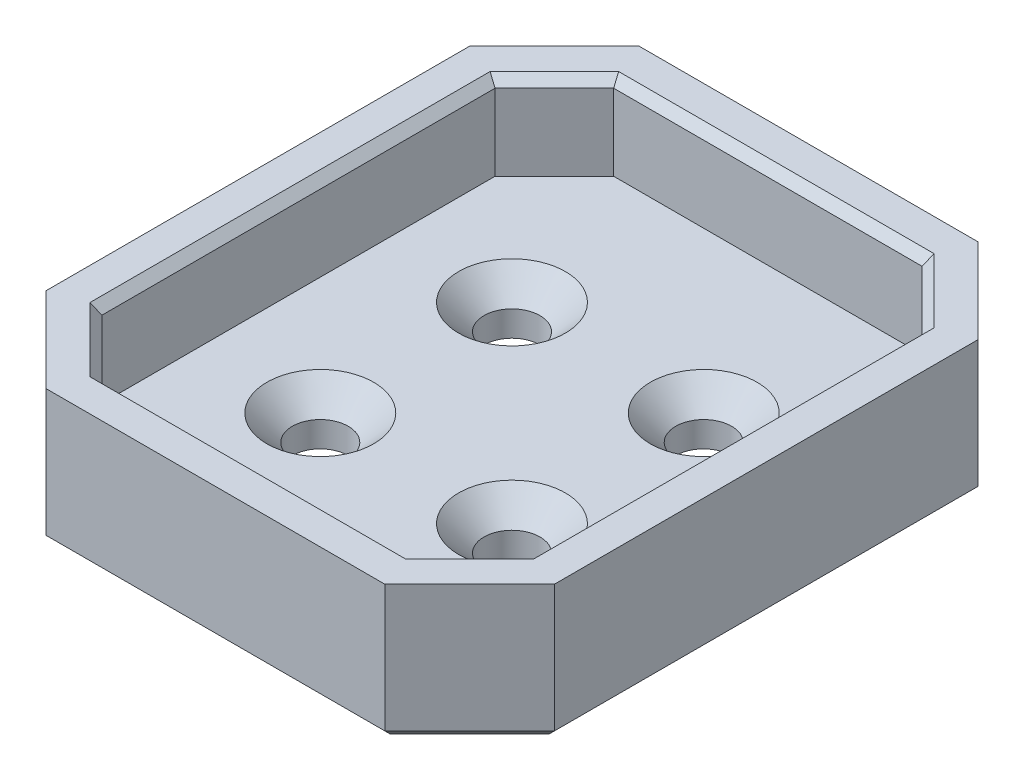
SolidWorks part; units mm, degrees
ref_plane "Front Plane" through (0, 0, 0) normal (0, 0, 1) x (1, 0, 0)
ref_plane "Top Plane" through (0, 0, 0) normal (0, 1, 0) x (1, 0, 0)
ref_plane "Right Plane" through (0, 0, 0) normal (1, 0, 0) x (0, 0, -1)
sketch "Sketch1" plane through (0, 0, 0) normal (0, 1, 0) x (1, 0, 0)
  line L1 (-15, -17.5) -> (15, -17.5)
  line L2 (-15, -17.5) -> (-15, 17.5)
  line L3 (-15, 17.5) -> (15, 17.5)
  line L4 (15, -17.5) -> (15, 17.5)
  line L5 (-15, -17.5) -> (15, 17.5) construction
  line L6 (-15, 17.5) -> (15, -17.5) construction
  point P0 (0, 0)
  dimension "D1" = 35
  dimension "D2" = 30
extrude "Boss-Extrude1" add sketch "Sketch1" along normal blind 3
sketch "Sketch2" plane through (0, 3, 0) normal (0, 1, 0) x (1, 0, 0)
  line L1 (12.6, -11.6) -> (12.6, 11.6)
  line L2 (9.1, 15.1) -> (-9.1, 15.1)
  line L3 (-12.6, 11.6) -> (-12.6, -11.6)
  line L4 (-9.1, -15.1) -> (9.1, -15.1)
  line L5 (15, -17.5) -> (15, 17.5)
  line L6 (15, 17.5) -> (-15, 17.5)
  line L7 (-15, 17.5) -> (-15, -17.5)
  line L8 (-15, -17.5) -> (15, -17.5)
  line L9 (15, -17.5) -> (15, 17.5)
  line L10 (15, 17.5) -> (-15, 17.5)
  line L11 (-15, 17.5) -> (-15, -17.5)
  line L12 (-15, -17.5) -> (15, -17.5)
  line L13 (12.6, 15.1) -> (-12.6, 15.1) construction
  line L14 (-12.6, 15.1) -> (-12.6, -15.1) construction
  line L15 (-9.1, 15.1) -> (-12.6, 11.6)
  line L16 (12.6, -15.1) -> (12.6, 15.1) construction
  line L17 (12.6, 11.6) -> (9.1, 15.1)
  line L18 (-12.6, -15.1) -> (12.6, -15.1) construction
  line L19 (9.1, -15.1) -> (12.6, -11.6)
  line L20 (-12.6, -11.6) -> (-9.1, -15.1)
  dimension "D3" = 3.5
  dimension "D4" = 3.5
  dimension "D1" = 0
  dimension "D2" = 2.4
extrude "Boss-Extrude2" add sketch "Sketch2" along normal blind 5
chamfer "Chamfer1" distance 5 angle 45 4 edges at (15, 4, 17.5) (-15, 4, 17.5) (15, 4, -17.5) (-15, 4, -17.5)
sketch "Sketch4" plane through (0, 3, 0) normal (0, 1, 0) x (1, 0, 0)
  line L0 (-5.6569, 5.6569) -> (0, 0) construction
  line L1 (0, 0) -> (0, 15.1) construction
  line L2 (9.1, 15.1) -> (-9.1, 15.1) construction
  circle A0 centre (0, 0) radius 8 construction
  circle A1 centre (-5.6569, 5.6569) radius 1.5
  circle A2 centre (5.6569, 5.6569) radius 1.5
  circle A3 centre (5.6569, -5.6569) radius 1.5
  circle A4 centre (-5.6569, -5.6569) radius 1.5
  point P16 (0, 0)
  dimension "D1" = 16
  dimension "D3" = 3
  dimension "D2" = 45
  dimension "D4" = 4
hole_wizard "CSK for M3 Flat Head Machine Screw1" positions "Sketch5" profile "Sketch6" countersink size "M3" standard "ANSI Metric" end condition through all
sketch "Sketch5" plane through (0, 3, 0) normal (0, 1, 0) x (1, 0, 0)
  point P4 (-5.6569, 5.6569)
  point P7 (5.6569, 5.6569)
  point P10 (5.6569, -5.6569)
  point P13 (-5.6569, -5.6569)
sketch "Sketch6" plane through (-5.6569, 3, -5.6569) normal (1, 0, 0) x (0, 0, 1)
  line L0 (0, 0) -> (0, 3)
  line L1 (0, 3) -> (1.65, 3)
  line L2 (1.65, 3) -> (1.65, 1.5)
  line L3 (1.65, 1.5) -> (3.15, 0)
  line L5 (3.15, 0) -> (0, 0)
  line L6 (-1.65, 1.5) -> (-3.15, 0) construction
  line L11 (0, -6.35) -> (0, 107.95) construction
  dimension "Thru Hole Dia." = 3.3
  dimension "Thru Hole Depth" = 3
  dimension "Near C'Sink Dia." = 6.3
  dimension "Near C'Sink Angle" = 90
chamfer "Chamfer2" distance 0.5 angle 45 8 edges at (10.85, 8, -13.35) (12.6, 8, 0) (10.85, 8, 13.35) (0, 8, 15.1) (-10.85, 8, 13.35) (-12.6, 8, 0) (0, 8, -15.1) (-10.85, 8, -13.35)
chamfer "Chamfer3" distance 0.5 angle 45 8 edges at (-12.5, 0, 15) (0, 0, 17.5) (12.5, 0, 15) (15, 0, 0) (12.5, 0, -15) (0, 0, -17.5) (-12.5, 0, -15) (-15, 0, 0)
